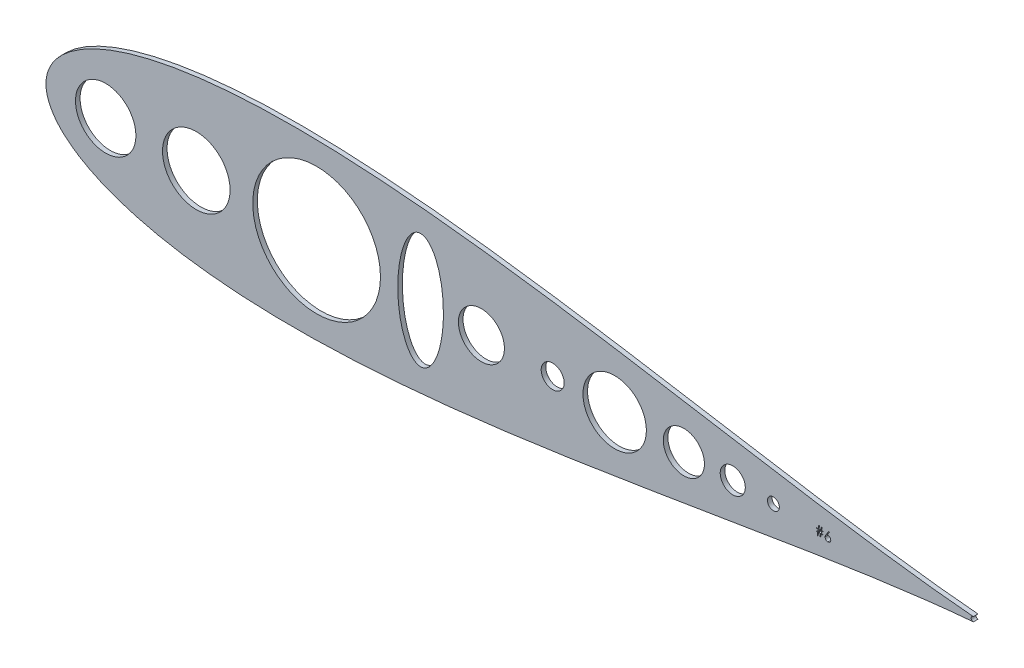
SolidWorks part; units mm, degrees
ref_plane "Front Plane" through (0, 0, 0) normal (0, 0, 1) x (1, 0, 0)
ref_plane "Top Plane" through (0, 0, 0) normal (0, 1, 0) x (1, 0, 0)
ref_plane "Right Plane" through (0, 0, 0) normal (1, 0, 0) x (0, 0, -1)
sketch "Sketch2" plane through (0, 0, 0) normal (0, 0, 1) x (1, 0, 0)
  line L0 (727.8331, 509.2636) -> (726.4908, 507.211)
  line L1 (727.482, 509.5393) -> (727.8331, 509.2636)
  line L2 (725.9657, 507.2212) -> (727.482, 509.5393)
  line L3 (724.2907, 507.5855) -> (723.4135, 507.5855)
  line L4 (724.2907, 507.9111) -> (724.2907, 507.5855)
  line L5 (723.4624, 507.9111) -> (724.2907, 507.9111)
  line L6 (723.7066, 509.5393) -> (723.4624, 507.9111)
  line L7 (723.3138, 509.5393) -> (723.7066, 509.5393)
  line L8 (723.0696, 507.9111) -> (723.3138, 509.5393)
  line L9 (722.0295, 507.9111) -> (723.0696, 507.9111)
  line L10 (722.2738, 509.5393) -> (722.0295, 507.9111)
  line L11 (721.881, 509.5393) -> (722.2738, 509.5393)
  line L12 (721.6367, 507.9111) -> (721.881, 509.5393)
  line L13 (720.6435, 507.9111) -> (721.6367, 507.9111)
  line L14 (720.6435, 507.5855) -> (720.6435, 507.9111)
  line L15 (721.5879, 507.5855) -> (720.6435, 507.5855)
  line L16 (721.4118, 506.4132) -> (721.5879, 507.5855)
  line L17 (720.5133, 506.4132) -> (721.4118, 506.4132)
  line L18 (720.5133, 506.0876) -> (720.5133, 506.4132)
  line L19 (721.363, 506.0876) -> (720.5133, 506.0876)
  line L20 (721.0994, 504.3291) -> (721.363, 506.0876)
  line L21 (721.4933, 504.3291) -> (721.0994, 504.3291)
  line L22 (721.7568, 506.0876) -> (721.4933, 504.3291)
  line L23 (722.7958, 506.0876) -> (721.7568, 506.0876)
  line L24 (722.5322, 504.3291) -> (722.7958, 506.0876)
  line L25 (722.9261, 504.3291) -> (722.5322, 504.3291)
  line L26 (723.1896, 506.0876) -> (722.9261, 504.3291)
  line L27 (724.1605, 506.0876) -> (723.1896, 506.0876)
  line L28 (724.1605, 506.4132) -> (724.1605, 506.0876)
  line L29 (723.2385, 506.4132) -> (724.1605, 506.4132)
  line L30 (723.4135, 507.5855) -> (723.2385, 506.4132)
  line L31 (723.0207, 507.5855) -> (721.9807, 507.5855)
  line L32 (722.8447, 506.4132) -> (723.0207, 507.5855)
  line L33 (721.8057, 506.4132) -> (722.8447, 506.4132)
  line L34 (721.9807, 507.5855) -> (721.8057, 506.4132)
  arc A0 (807.168, 506.1079) -> (807.2931, 506.1246) centre (807.0631, 507.3687) ccw
  arc A1 (807.2963, 508.6123) -> (807.2931, 506.1246) centre (807.2947, 507.3684) ccw
  circle A2 centre (328.0596, 507.3687) radius 16.6848
  circle A3 centre (696.8327, 507.3687) radius 3.2907
  circle A4 centre (674.3907, 507.3687) radius 6.9292
  circle A5 centre (647.3866, 507.3687) radius 11.3532
  circle A6 centre (535.5664, 507.3687) radius 12.7
  circle A7 centre (378.0864, 507.3687) radius 18.669
  circle A8 centre (444.5488, 507.3687) radius 35.2696
  circle A9 centre (609.1648, 507.3687) radius 17.5111
  circle A10 centre (574.9364, 507.3687) radius 6.35
  arc A11 (807.2963, 508.6123) -> (807.168, 508.6296) centre (807.0631, 507.3687) ccw
  ellipse E0 centre (501.9977, 507.3687) end of major axis (501.9977, 539.226) minor radius 12.6216
  spline S0 degree 3 poles (807.168, 508.6296) (806.7556, 508.6639) (803.6475, 508.9257) (797.5266, 509.4915) (788.4411, 510.4366) (778.3677, 511.5964) (767.3443, 512.9777) (755.4224, 514.5821) (742.6536, 516.4059) (729.093, 518.4396) (714.7983, 520.6689) (699.8294, 523.0737) (684.2482, 525.6293) (668.1182, 528.3063) (651.5048, 531.0707) (634.4746, 533.8852) (617.0958, 536.7089) (599.4377, 539.4984) (581.5711, 542.2084) (563.5679, 544.7922) (545.5012, 547.2027) (527.4456, 549.3927) (509.4769, 551.3163) (491.6721, 552.9289) (474.1097, 554.1886) (456.8692, 555.0565) (440.0317, 555.4976) (423.6795, 555.4812) (407.8958, 554.9814) (392.7656, 553.9787) (378.3752, 552.4585) (364.8124, 550.4139) (352.1677, 547.8442) (340.5347, 544.758) (330.0117, 541.1735) (320.7037, 537.1225) (312.7237, 532.6587) (306.191, 527.8727) (301.2155, 522.9208) (297.8469, 518.0648) (295.9686, 513.6837) (295.2101, 510.1692) (295.0373, 507.3687) (295.2101, 504.5682) (295.9686, 501.0538) (297.8469, 496.6727) (301.2155, 491.8167) (306.191, 486.8648) (312.7237, 482.0788) (320.7037, 477.615) (330.0117, 473.564) (340.5347, 469.9794) (352.1677, 466.8933) (364.8124, 464.3236) (378.3752, 462.279) (392.7656, 460.7588) (407.8958, 459.756) (423.6795, 459.2563) (440.0317, 459.2399) (456.8692, 459.6809) (474.1097, 460.5488) (491.6721, 461.8086) (509.4769, 463.4212) (527.4456, 465.3448) (545.5012, 467.5348) (563.5679, 469.9453) (581.5711, 472.5291) (599.4377, 475.2391) (617.0958, 478.0286) (634.4746, 480.8523) (651.5048, 483.6668) (668.1182, 486.4312) (684.2482, 489.1081) (699.8294, 491.6638) (714.7983, 494.0686) (729.093, 496.2979) (742.6536, 498.3316) (755.4224, 500.1554) (767.3443, 501.7597) (778.3677, 503.1411) (788.4411, 504.3009) (797.5266, 505.246) (803.6475, 505.8118) (806.7556, 506.0736) (807.168, 506.1079) knots 0.020157 0.020157 0.020157 0.020157 0.021271 0.028553 0.036781 0.04592 0.055932 0.066773 0.078397 0.090755 0.103793 0.117456 0.131686 0.146422 0.1616 0.177156 0.193024 0.209135 0.225421 0.241812 0.258238 0.274629 0.290914 0.307025 0.322893 0.338448 0.353626 0.368361 0.38259 0.396253 0.40929 0.421647 0.43327 0.444109 0.454119 0.463255 0.471479 0.478755 0.485052 0.490344 0.49461 0.497833 0.5 0.502167 0.50539 0.509656 0.514948 0.521245 0.528521 0.536745 0.545881 0.555891 0.56673 0.578353 0.59071 0.603747 0.61741 0.631639 0.646374 0.661552 0.677107 0.692975 0.709086 0.725371 0.741762 0.758188 0.774579 0.790865 0.806976 0.822844 0.8384 0.853578 0.868314 0.882544 0.896207 0.909245 0.921603 0.933227 0.944068 0.95408 0.963219 0.971447 0.978729 0.979843 0.979843 0.979843 0.979843
  spline S1 degree 3 poles (726.4908, 507.211) (726.5802, 507.2253) (726.7545, 507.253) (726.9309, 507.2576) (727.0169, 507.2599) knots 0 0 0 0 0.512659 1 1 1 1
  spline S2 degree 3 poles (728.524, 505.7548) (728.522, 505.6837) (728.5179, 505.5438) (728.4774, 505.3401) (728.4145, 505.146) (728.3245, 504.9646) (728.2128, 504.7962) (728.0765, 504.647) (727.9206, 504.514) (727.7443, 504.4027) (727.5545, 504.3119) (727.3551, 504.2466) (727.1481, 504.2064) (727.0076, 504.2014) (726.9365, 504.1988) knots 0 0 0 0 0.085948 0.169125 0.250399 0.33229 0.413364 0.494172 0.576022 0.660757 0.745783 0.830044 0.914028 1 1 1 1
  spline S3 degree 3 poles (725.3979, 505.7456) (725.3996, 505.7979) (725.4031, 505.9048) (725.4276, 506.0665) (725.4668, 506.2321) (725.5108, 506.3725) (725.5573, 506.4876) (725.596, 506.5803) (725.6441, 506.6758) (725.6955, 506.7772) (725.7546, 506.8819) (725.819, 506.9918) (725.8902, 507.1051) (725.9402, 507.1819) (725.9657, 507.2212) knots 0 0 0 0 0.097818 0.199726 0.305276 0.415811 0.474472 0.537274 0.603657 0.674299 0.749834 0.828598 0.912378 1 1 1 1
  spline S4 degree 3 poles (726.9365, 504.1988) (726.8682, 504.2011) (726.7328, 504.2054) (726.5336, 504.2446) (726.3422, 504.308) (726.16, 504.3954) (725.9911, 504.5058) (725.8401, 504.6387) (725.7076, 504.7913) (725.5973, 504.9635) (725.5098, 505.1485) (725.4443, 505.3415) (725.4059, 505.5416) (725.4006, 505.6773) (725.3979, 505.7456) knots 0 0 0 0 0.084335 0.167052 0.249566 0.33274 0.415915 0.497828 0.580373 0.6646 0.749467 0.83251 0.915639 1 1 1 1
  spline S5 degree 3 poles (727.0169, 507.2599) (727.0686, 507.2585) (727.1702, 507.2557) (727.3194, 507.2347) (727.4628, 507.2016) (727.5998, 507.1533) (727.7308, 507.0916) (727.8566, 507.0177) (727.9749, 506.9277) (728.0872, 506.8271) (728.1891, 506.7158) (728.2794, 506.5976) (728.3552, 506.4728) (728.4167, 506.3414) (728.4644, 506.2035) (728.4992, 506.0595) (728.5198, 505.909) (728.5226, 505.8068) (728.524, 505.7548) knots 0 0 0 0 0.065231 0.128405 0.190067 0.250943 0.311546 0.372863 0.435024 0.499072 0.563091 0.62551 0.68668 0.747283 0.808563 0.870742 0.934341 1 1 1 1
  spline S6 degree 3 poles (725.8538, 505.7273) (725.8547, 505.693) (725.8565, 505.6257) (725.8727, 505.5265) (725.8974, 505.431) (725.9342, 505.3398) (725.978, 505.2514) (726.036, 505.1691) (726.1001, 505.0878) (726.1769, 505.0137) (726.2592, 504.9449) (726.3471, 504.8847) (726.4388, 504.8332) (726.5354, 504.7928) (726.6356, 504.7597) (726.7403, 504.7363) (726.8494, 504.7232) (726.9233, 504.721) (726.961, 504.7199) knots 0 0 0 0 0.061842 0.121262 0.180746 0.239231 0.298308 0.358183 0.420359 0.484792 0.549938 0.613718 0.676681 0.739154 0.8022 0.86674 0.93205 1 1 1 1
  spline S7 degree 3 poles (728.0681, 505.7273) (728.0673, 505.762) (728.0658, 505.8301) (728.0481, 505.9298) (728.0235, 506.026) (727.9863, 506.1183) (727.9381, 506.2061) (727.8793, 506.29) (727.8114, 506.3705) (727.7328, 506.4454) (727.6474, 506.5138) (727.5565, 506.5742) (727.4614, 506.6252) (727.3622, 506.6677) (727.2578, 506.6984) (727.1498, 506.7226) (727.0369, 506.7355) (726.9603, 506.7377) (726.9213, 506.7388) knots 0 0 0 0 0.061138 0.119994 0.178225 0.236256 0.294929 0.354716 0.41673 0.480664 0.545832 0.609758 0.672971 0.736017 0.799839 0.864775 0.931088 1 1 1 1
  spline S8 degree 3 poles (726.9213, 506.7388) (726.8826, 506.7377) (726.807, 506.7355) (726.6961, 506.7227) (726.5911, 506.6986) (726.4907, 506.6678) (726.3968, 506.6256) (726.3085, 506.5743) (726.2257, 506.5139) (726.1491, 506.4452) (726.0797, 506.3701) (726.02, 506.2896) (725.9684, 506.2056) (725.9265, 506.1176) (725.8938, 506.0255) (725.8702, 505.9298) (725.8571, 505.8298) (725.8549, 505.7619) (725.8538, 505.7273) knots 0 0 0 0 0.070599 0.137901 0.203196 0.26679 0.329106 0.390654 0.452653 0.515748 0.577926 0.63893 0.698351 0.757296 0.816394 0.876267 0.936817 1 1 1 1
  spline S9 degree 3 poles (726.961, 504.7199) (726.9987, 504.721) (727.0726, 504.7232) (727.1817, 504.7363) (727.2863, 504.7597) (727.3865, 504.7928) (727.4831, 504.8332) (727.5747, 504.8843) (727.6618, 504.9452) (727.7442, 505.0136) (727.8206, 505.0882) (727.8863, 505.1684) (727.9424, 505.2521) (727.9881, 505.3395) (728.0244, 505.4311) (728.0493, 505.5265) (728.0654, 505.6257) (728.0672, 505.693) (728.0681, 505.7273) knots 0 0 0 0 0.067962 0.133283 0.197835 0.260892 0.323377 0.38635 0.449638 0.514795 0.57924 0.641814 0.701359 0.760727 0.819222 0.878716 0.938147 1 1 1 1
extrude "Boss-Extrude1" add sketch "Sketch2" along normal blind 2.54 contours A11 S0 A0 A1 L3 L30 L29 L28 L27 L26 L25 L24 L23 L22 L21 L20 L19 L18 L17 L16 L15 L14 L13 L12 L11 L10 L9 L8 L7 L6 L5 L4 A2 A3 A4 A5 A6 A7 A8 A9 A10
